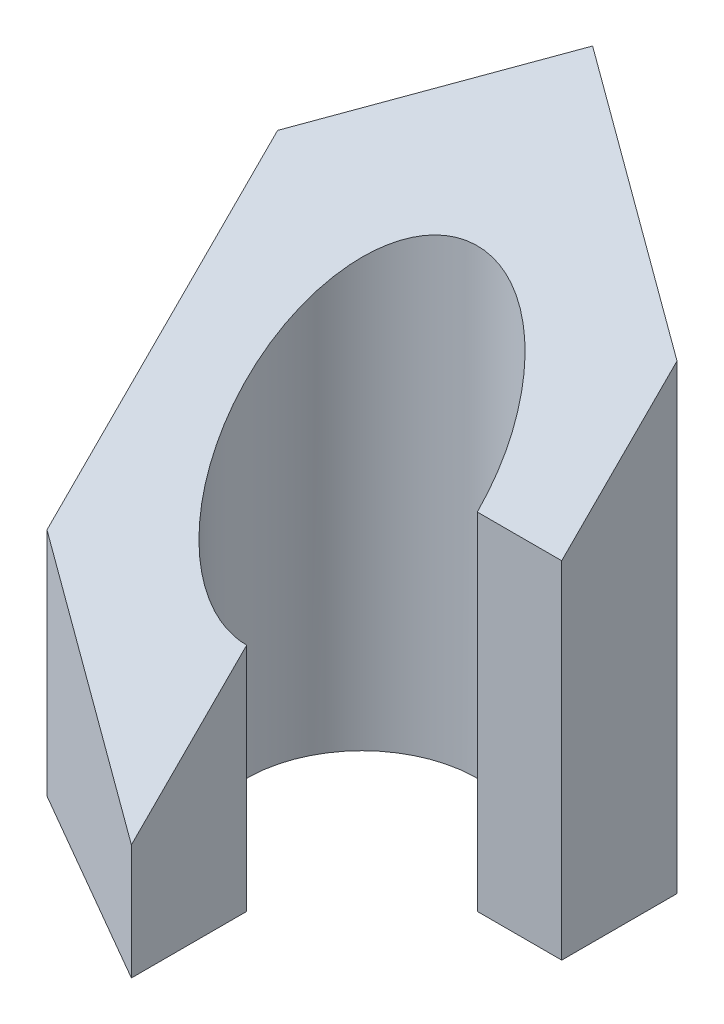
SolidWorks part; units mm, degrees
ref_plane "Front Plane" through (0, 0, 0) normal (0, 0, 1) x (1, 0, 0)
ref_plane "Top Plane" through (0, 0, 0) normal (0, 1, 0) x (1, 0, 0)
ref_plane "Right Plane" through (0, 0, 0) normal (1, 0, 0) x (0, 0, -1)
sketch "Sketch1" plane through (0, 0, 0) normal (0, 1, 0) x (1, 0, 0)
  line L0 (2, 0) -> (3.4641, 0)
  line L1 (3.4641, 2) -> (0, 4)
  line L2 (0, 4) -> (-3.4641, 2)
  line L3 (-3.4641, 2) -> (-3.4641, -2)
  line L4 (-3.4641, -2) -> (0, -4)
  line L6 (3.4641, 0) -> (3.4641, 2)
  line L7 (0, -2) -> (0, -4)
  line L9 (0, -4) -> (1.7321, -3) [skipped]
  arc A0 (3.4641, 0) -> (0, -3.4641) centre (0, 0) ccw construction
  arc A1 (2, 0) -> (0, -2) centre (0, 0) ccw
  dimension "D2" = 4
  dimension "D1" = 4
extrude "Boss-Extrude1" add sketch "Sketch1" along normal blind 10
sketch "Sketch3" plane through (0, 0, 0) normal (1, 0, 0) x (0, 0, -1)
  line L0 (-4, 2) -> (4, 10)
  line L1 (-4, 10) -> (-4, 0) construction
  line L2 (4, 10) -> (-4, 10)
  line L3 (-4, 10) -> (-4, 2)
  dimension "D1" = 2
extrude "Cut-Extrude2" cut sketch "Sketch3" against normal blind 10 and the other way blind 10
